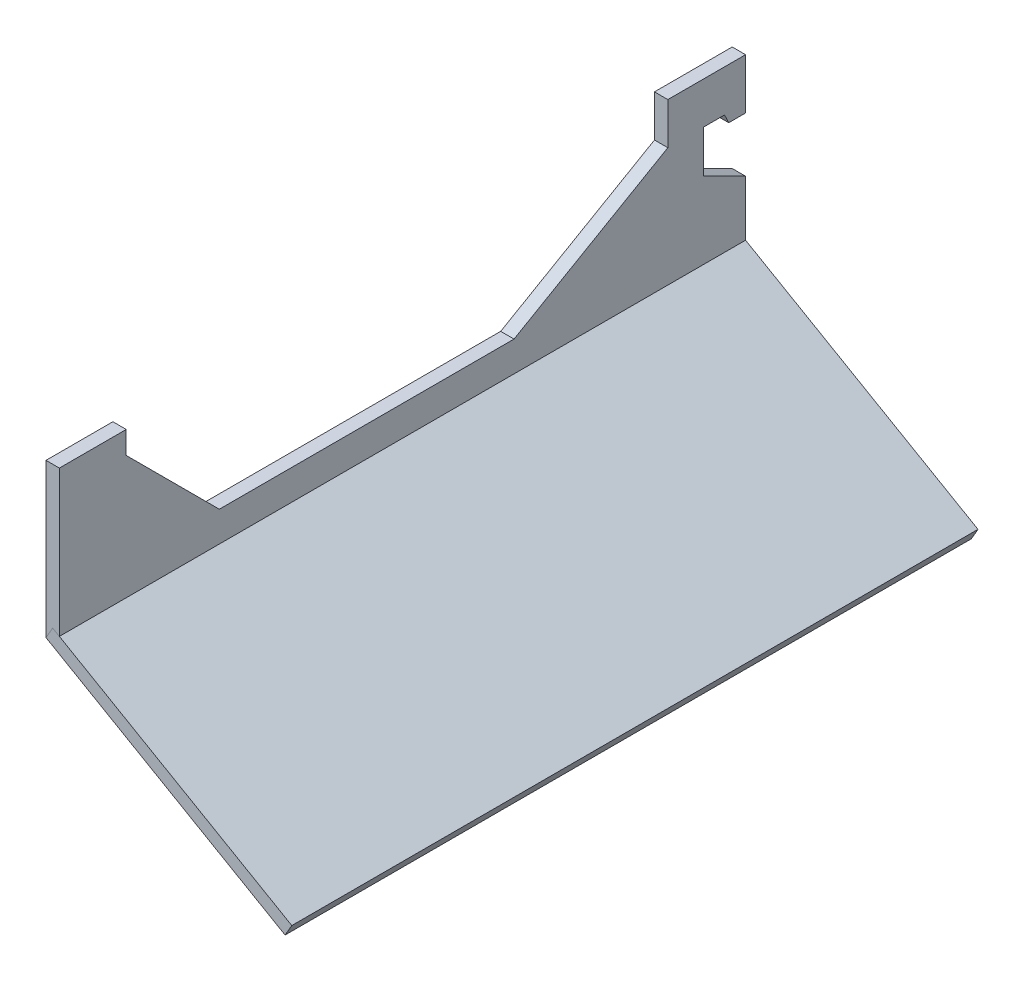
SolidWorks part; units mm, degrees
ref_plane "Front Plane" through (0, 0, 0) normal (0, 0, 1) x (1, 0, 0)
ref_plane "Top Plane" through (0, 0, 0) normal (0, 1, 0) x (1, 0, 0)
ref_plane "Right Plane" through (0, 0, 0) normal (1, 0, 0) x (0, 0, -1)
sketch "Sketch6" plane through (0, 0, 0) normal (0, 1, 0) x (1, 0, 0)
  line L0 (0, -218.7522) -> (0, 116.8814) construction
sketch "Sketch9" plane through (0, 0, 0) normal (1, 0, 0) x (0, 0, -1)
  line L0 (37.6238, 70.8385) -> (37.6238, 7.9992) construction
  line L1 (51.1496, 71.1243) -> (51.1496, 8.285) construction
  line L2 (65.9911, 71.1243) -> (65.9911, 8.285) construction
  line L3 (79.3028, 71.1243) -> (79.3028, 8.2774) construction
  line L4 (93.104, 70.9385) -> (93.104, 8.0915) construction
  line L5 (108.8651, 7.9915) -> (108.8651, 70.8446) construction
  line L6 (126.2304, 71.1243) -> (126.2304, 8.2774) construction
  line L7 (134.6212, 7.9657) -> (134.6212, 70.8175) construction
  line L8 (19.8849, 61.8648) -> (19.8849, 60.5648) construction
  line L9 (19.8849, 61.8648) -> (140.5349, 61.8648) construction
  line L10 (19.8849, 11.0648) -> (140.5349, 11.0648) construction
  line L11 (19.8849, 60.5648) -> (19.8849, 56.9648) construction
  line L12 (19.8849, 36.4648) -> (140.5349, 36.4648) construction
  line L13 (19.8849, 47.4648) -> (140.5349, 47.4648) construction
  line L14 (19.8849, 25.4648) -> (140.5349, 25.4648) construction
  line L15 (19.8849, 15.9648) -> (140.5349, 15.9648) construction
  line L16 (19.8849, 56.9648) -> (140.5349, 56.9648) construction
  line L17 (24.4126, 70.8385) -> (24.4126, 7.9992)
  line L18 (19.8849, 12.3648) -> (140.5349, 12.3648) construction
  line L19 (19.8849, 60.5648) -> (140.5349, 60.5648) construction
  line L20 (140.5349, 61.8648) -> (140.5349, 60.5648) construction
  line L21 (-218.7522, 0) -> (116.8814, 0) construction
  line L22 (140.5349, 60.5648) -> (140.5349, 56.9648) construction
  line L23 (140.5349, 56.9648) -> (140.5349, 47.4648) construction
  line L24 (140.5349, 47.4648) -> (140.5349, 36.4648) construction
  line L25 (140.5349, 36.4648) -> (140.5349, 25.4648) construction
  line L26 (140.5349, 25.4648) -> (140.5349, 15.9648) construction
  line L27 (140.5349, 15.9648) -> (140.5349, 12.3648) construction
  line L28 (140.5349, 12.3648) -> (140.5349, 11.0648) construction
  line L29 (19.8849, 56.9648) -> (19.8849, 47.4648) construction
  line L30 (19.8849, 47.4648) -> (19.8849, 36.4648) construction
  line L31 (19.8849, 36.4648) -> (19.8849, 25.4648) construction
  line L32 (19.8849, 25.4648) -> (19.8849, 15.9648) construction
  line L33 (19.8849, 15.9648) -> (19.8849, 12.3648) construction
  line L34 (19.8849, 12.3648) -> (19.8849, 11.0648) construction
  spline S0 degree 3 poles (51.2996, 60.9306) (65.3231, 61.9876) (79.6239, 62.1542) (93.583, 60.8224) (110.3999, 56.9428) (123.3769, 51.8767) (135.0763, 45.9483) (143.4183, 36.2774) (135.0505, 27.8617) (123.4214, 21.8328) (110.225, 15.7356) (93.6714, 12.1328) (79.5289, 10.8674) (65.4121, 10.9017) (51.0743, 12.0654) (37.6053, 14.9428) (23.9138, 23.9186) (18.0793, 36.4535) (24.0546, 49.1584) (37.259, 57.8231) (51.2996, 60.9306) (65.3231, 61.9876) (79.6239, 62.1542) knots -0.161453 -0.105693 -0.054332 0 0.047894 0.097672 0.154194 0.222755 0.257069 0.295416 0.33342 0.367649 0.435779 0.492752 0.542693 0.590587 0.644732 0.696926 0.751601 0.795074 0.838547 0.894307 0.945668 1 1.047894 1.097672 1.154194 only from (65.9911, 61.8648) to (65.9911, 61.8648)
  point P22 (50.9779, 12.2648)
  point P24 (50.9779, 60.6648)
  dimension "D10" = 11.0648
  dimension "D1" = 50.8
  dimension "D2" = 120.65
  dimension "D3" = 11
  dimension "D4" = 11
  dimension "D5" = 20.5
  dimension "D6" = 20.5
  dimension "D7" = 24.1
  dimension "D8" = 24.1
ref_plane "Plane3" through (0, 0, 0) normal (-0.5, -0.866, 0) x (0, 0, -1)
sketch "Sketch10" plane through (0, 0, 0) normal (1, 0, 0) x (0, 0, -1)
  line L0 (15.8849, 36.4648) -> (0, 36.4648)
  line L1 (0, 36.4648) -> (0, 0)
  line L2 (-218.7522, 0) -> (116.8814, 0) construction
  line L3 (0, 0) -> (163, 0)
  line L4 (111.8843, 0) -> (-111.8843, 0) construction
  line L5 (163, 0) -> (163, 15)
  line L7 (144.5349, 36.4648) -> (144.5349, 30.0934)
  line L8 (144.5349, 30.0934) -> (108, 9)
  line L9 (108, 9) -> (38, 9)
  line L10 (38, 9) -> (15.8849, 31.1151)
  line L11 (15.8849, 31.1151) -> (15.8849, 36.4648)
  line L12 (144.5349, 36.4648) -> (144.5349, 40)
  line L15 (153, 20) -> (163, 15)
  line L16 (153, 40) -> (153, 0) construction
  line L17 (140.5349, 36.4648) -> (163, 36.4648) construction
  line L21 (163, 40) -> (163, 28)
  line L22 (163, 28) -> (159, 28)
  line L23 (159, 28) -> (158, 30.0934)
  line L24 (158, 30.0934) -> (153, 30.0934)
  line L25 (153, 30.0934) -> (153, 20)
  line L26 (144.5349, 40) -> (153, 40)
  line L27 (153, 40) -> (163, 40)
  point P18 (0, 0)
  point P26 (163.2961, 14.3621)
  point P30 (153, 20.6543)
  point P31 (163, 14.2637)
  dimension "D1" = 4
  dimension "D2" = 9
  dimension "D3" = 4
  dimension "D4" = 40
  dimension "D5" = 225
  dimension "D6" = 240
  dimension "D7" = 70
  dimension "D8" = 38
  dimension "D9" = 4
  dimension "D10" = 5
  dimension "D11" = 55
  dimension "D12" = 10
  dimension "D13" = 12
  dimension "D14" = 20
  dimension "D15" = 15
extrude "Boss-Extrude1" add sketch "Sketch10" along normal blind 3.175
sketch "Sketch11" plane through (0, 0, 0) normal (-0.5, -0.866, 0) x (0, 0, -1)
  line L1 (163, 0) -> (0, 0)
  line L2 (163, 0) -> (163, 65.5808)
  line L3 (163, 65.5808) -> (0, 65.5808)
  line L4 (0, 0) -> (0, 65.5808)
extrude "Boss-Extrude2" add sketch "Sketch11" against normal blind 3.175 separate body
ref_plane "Plane2" through (45, 0, 0) normal (1, 0, 0) x (0, 0, -1)
sketch "Sketch5" plane through (0, 19.2012, 184.6399) normal (1, 0, 0) x (0, 0, -1)
  line L2 (204.3693, -19.2012) -> (184.3693, 4.2988)
  line L4 (184.3693, 29.2988) -> (204.3693, 52.7988)
  line L10 (131.5763, 16.7988) -> (15.8268, 16.7988) construction
  line L11 (247.3693, 5.4691) -> (247.3693, -92.3775) construction
  line L12 (204.3693, -100.7007) -> (204.3693, 68.0605) construction
  line L13 (184.3693, 4.2988) -> (184.3693, 29.2988)
  line L16 (247.3693, 42.7988) -> (265.3693, 42.7988)
  line L17 (265.3693, 42.7988) -> (265.3693, 52.7988)
  line L18 (265.3693, 52.7988) -> (204.3693, 52.7988)
  line L19 (204.3693, -19.2012) -> (265.3693, -19.2012)
  line L20 (265.3693, -19.2012) -> (265.3693, -9.2012)
  line L21 (265.3693, -9.2012) -> (247.3693, -9.2012)
  line L22 (-34.1123, -19.2012) -> (301.5213, -19.2012) construction
  ellipse E0 centre (247.3693, 16.7988) end of major axis (204.3693, 16.7988) minor radius 26 (247.3693, -9.2012) -> (247.3693, 42.7988) cw
  point P0 (184.3693, 16.7988)
  point P29 (105.2094, 0.142)
  point P34 (105.2094, -19.858)
  dimension "D2" = 20
  dimension "D7" = 25
  dimension "D1" = 26
  dimension "D3" = 43
  dimension "D4" = 10
  dimension "D5" = 10
  dimension "D6" = 18
sketch "Sketch8" plane through (0, 0, 0) normal (1, 0, 0) x (0, 0, -1)
  line L0 (318.4214, 400.3917) -> (1509.088, 400.3917) construction
